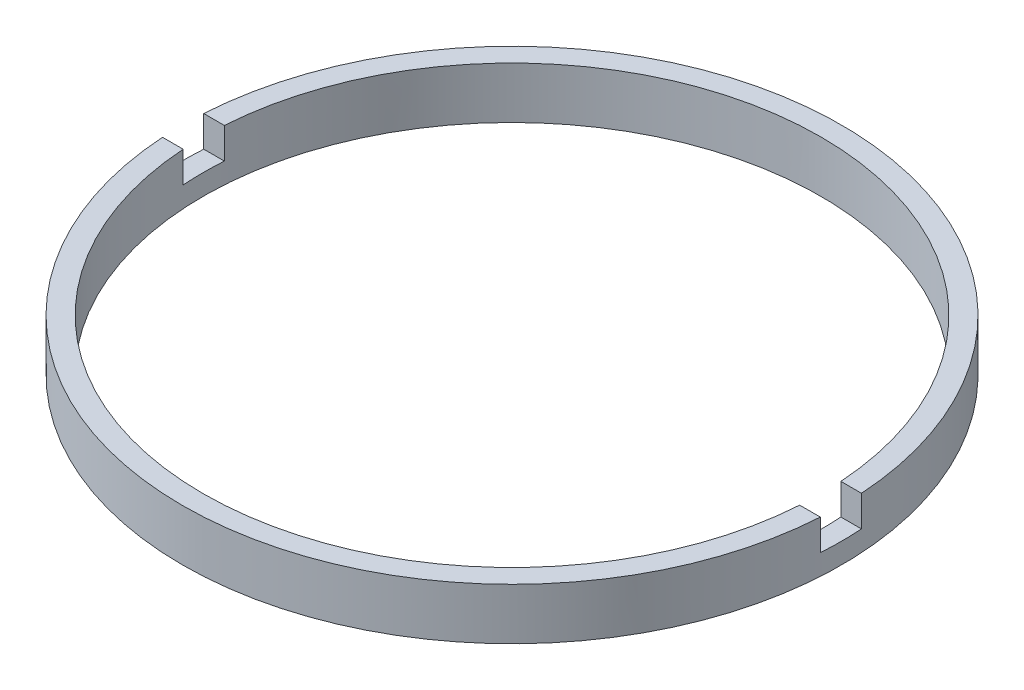
SolidWorks part; units mm, degrees
ref_plane "前视基准面" through (0, 0, 0) normal (0, 0, 1) x (1, 0, 0)
ref_plane "上视基准面" through (0, 0, 0) normal (0, 1, 0) x (1, 0, 0)
ref_plane "右视基准面" through (0, 0, 0) normal (1, 0, 0) x (0, 0, -1)
sketch "草图1" plane through (0, 0, 0) normal (0, 0, 1) x (1, 0, 0)
  line L0 (0, 56.2608) -> (0, -99.1922) construction
  line L1 (15, -1.9642) -> (16, -1.9642)
  line L4 (16, -1.9642) -> (16, -4.4642)
  line L5 (15, -4.4642) -> (15, -1.9642)
  line L7 (15, -4.4642) -> (16, -4.4642)
  dimension "D1" = 2.5
  dimension "D2" = 16
  dimension "D3" = 15
revolve "旋转1" add sketch "草图1" angle 360 about L0
cosmetic thread "装饰螺纹线1" parameters "D2"=30.9
sketch "草图2" plane through (0, -1.9642, 0) normal (0, 1, 0) x (1, 0, 0)
  line L0 (-28.67, 0) -> (29.9422, 0) construction
  line L2 (-26.8525, 1) -> (26.8525, 1)
  line L3 (-26.8525, 1) -> (-26.8525, -1)
  line L4 (-26.8525, -1) -> (26.8525, -1)
  line L5 (26.8525, 1) -> (26.8525, -1)
  line L6 (-26.8525, 1) -> (26.8525, -1) construction
  line L7 (-26.8525, -1) -> (26.8525, 1) construction
  point P3 (0, 0)
  dimension "D1" = 2
extrude "切除-拉伸1" cut sketch "草图2" against normal blind 1.5
